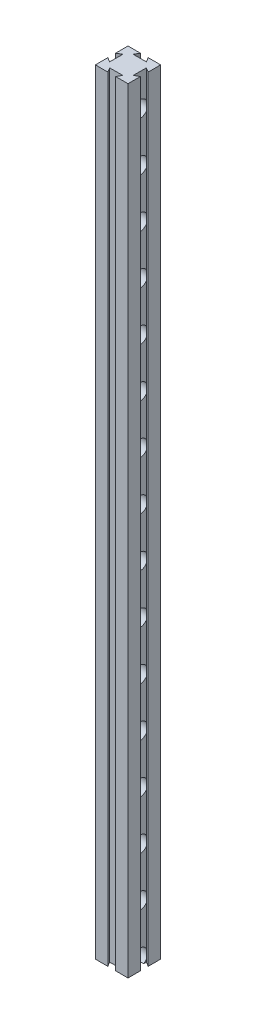
SolidWorks part; units mm, degrees
material "5052-H32"
ref_plane "Front Plane" through (0, 0, 0) normal (0, 0, 1) x (1, 0, 0)
ref_plane "Top Plane" through (0, 0, 0) normal (0, 1, 0) x (1, 0, 0)
ref_plane "Right Plane" through (0, 0, 0) normal (1, 0, 0) x (0, 0, -1)
sketch "Sketch1" plane through (0, 0, 0) normal (0, 1, 0) x (1, 0, 0)
  line L0 (-25, 25) -> (-5.9585, 25)
  line L1 (-5.9585, 25) -> (-10, 18)
  line L2 (-10, 18) -> (10, 18)
  line L3 (10, 18) -> (5.9585, 25)
  line L4 (5.9585, 25) -> (25, 25)
  line L5 (25, 25) -> (25, 5.9585)
  line L6 (25, 5.9585) -> (18, 10)
  line L7 (18, 10) -> (18, -10)
  line L8 (18, -10) -> (25, -5.9585)
  line L9 (25, -5.9585) -> (25, -25)
  line L10 (25, -25) -> (5.9585, -25)
  line L11 (5.9585, -25) -> (10, -18)
  line L12 (10, -18) -> (-10, -18)
  line L13 (-10, -18) -> (-5.9585, -25)
  line L14 (-5.9585, -25) -> (-25, -25)
  line L16 (-25, -25) -> (-25, -5.9585)
  line L17 (-25, -5.9585) -> (-18, -10)
  line L18 (-18, -10) -> (-18, 10)
  line L19 (-18, 10) -> (-25, 5.9585)
  line L20 (-25, 5.9585) -> (-25, 25)
  line L21 (0, 23.4558) -> (0, -31.0073) construction
  line L22 (-32.2836, 0) -> (31.3226, 0) construction
  point P30 (-18, 0)
  point P31 (0, 18)
  point P42 (0, -18)
  point P43 (18, 0)
  dimension "D2" = 20
  dimension "D3" = 7
  dimension "D4" = 7
  dimension "D5" = 7
  dimension "D6" = 7
  dimension "D7" = 20
  dimension "D8" = 60
  dimension "D9" = 50
  dimension "D10" = 60
  dimension "D11" = 50
  dimension "D12" = 60
  dimension "D13" = 60
  dimension "D14" = 60
  dimension "D15" = 60
  dimension "D16" = 60
extrude "Boss-Extrude1" add sketch "Sketch1" along normal blind 1186
sketch "Sketch3" plane through (0, 0, 0) normal (1, 0, 0) x (0, 0, -1)
  line L0 (-10, 1186) -> (10, 1186) construction
  line L1 (25, 1186) -> (25, 0) construction
  line L2 (0, 1796.6199) -> (0, -651.5569) construction
  circle A0 centre (0, 1136) radius 12.5
  circle A1 centre (0, 1061) radius 12.5
  circle A2 centre (0, 986) radius 12.5
  circle A3 centre (0, 911) radius 12.5
  circle A4 centre (0, 836) radius 12.5
  circle A5 centre (0, 761) radius 12.5
  circle A6 centre (0, 686) radius 12.5
  circle A7 centre (0, 611) radius 12.5
  circle A8 centre (0, 536) radius 12.5
  circle A9 centre (0, 461) radius 12.5
  circle A10 centre (0, 386) radius 12.5
  circle A11 centre (0, 311) radius 12.5
  circle A12 centre (0, 236) radius 12.5
  circle A13 centre (0, 161) radius 12.5
  circle A14 centre (0, 86) radius 12.5
  circle A15 centre (0, 11) radius 12.5
  circle A16 centre (0, -64) radius 12.5
  circle A17 centre (0, -139) radius 12.5
  circle A18 centre (0, -214) radius 12.5
  circle A19 centre (0, -289) radius 12.5
  circle A20 centre (0, -364) radius 12.5
  circle A21 centre (0, -439) radius 12.5
  circle A22 centre (0, -514) radius 12.5
  dimension "D1" = 25
  dimension "D2" = 50
  dimension "D3" = 25
  dimension "D4" = 23
extrude "Cut-Extrude1" cut sketch "Sketch3" against normal blind 18 and the other way blind 18
